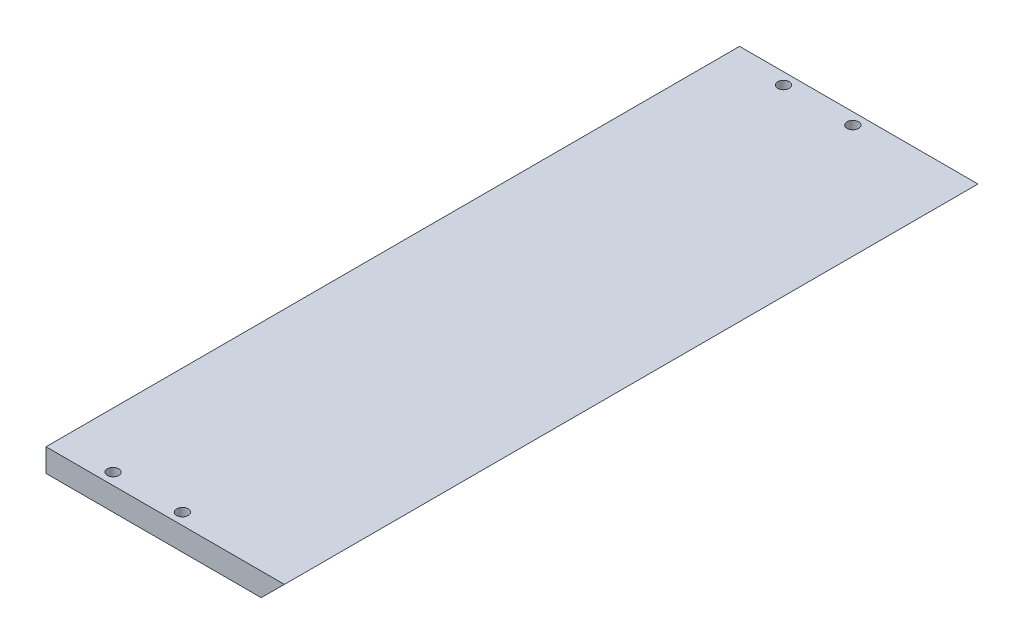
SolidWorks part; units mm, degrees
material "A286 Iron Base Superalloy"
ref_plane "Front Plane" through (0, 0, 0) normal (0, 0, 1) x (1, 0, 0)
ref_plane "Top Plane" through (0, 0, 0) normal (0, 1, 0) x (1, 0, 0)
ref_plane "Right Plane" through (0, 0, 0) normal (1, 0, 0) x (0, 0, -1)
sketch "Sketch1" plane through (0, 0, 0) normal (0, 0, 1) x (1, 0, 0)
  line L0 (51.57, 5) -> (46.53, 0)
  line L1 (0, 0) -> (46.53, 0)
  line L2 (0, 0) -> (0, 5)
  line L3 (0, 5) -> (51.57, 5)
  dimension "D1" = 5
  dimension "D2" = 46.53
  dimension "D3" = 51.57
extrude "Boss-Extrude1" add sketch "Sketch1" along normal mid plane 150
sketch "Sketch2" plane through (0, 5, 0) normal (0, 1, 0) x (1, 0, 0)
  line L0 (51.57, -75) -> (0, -75) construction
  line L1 (0, -75) -> (0, 75) construction
  circle A0 centre (12, -72.5) radius 1.5
  circle A1 centre (27, -72.5) radius 1.5
  dimension "D1" = 3
  dimension "D2" = 3
  dimension "D3" = 15
  dimension "D4" = 2.5
  dimension "D5" = 2.5
  dimension "D6" = 12
hole_wizard "M3x0.5 Tapped Hole1" positions "Sketch4" profile "Sketch3" tap size "M3x0.5" standard "ANSI Metric" end condition through all
sketch "Sketch4" plane through (0, 5, 0) normal (0, 1, 0) x (1, 0, 0)
  point P0 (12, -72.5)
  point P3 (27, -72.5)
sketch "Sketch3" plane through (12, 5, 72.5) normal (1, 0, 0) x (0, 0, 1)
  line L0 (0, 0) -> (0, 5)
  line L1 (0, 5) -> (1.25, 5)
  line L2 (1.25, 5) -> (1.25, 0)
  line L5 (1.25, 0) -> (0, 0)
  line L11 (0, -6.35) -> (0, 107.95) construction
  dimension "Thru Tap Drill Dia." = 2.5
  dimension "Thru Tap Drill Depth" = 5
cosmetic thread "Hole Thread1" parameters "D2"=3
cosmetic thread "Hole Thread2" parameters "D2"=3
mirror "Mirror1" about plane through (0, 0, 0) normal (0, 0, 1) of "M3x0.5 Tapped Hole1"
